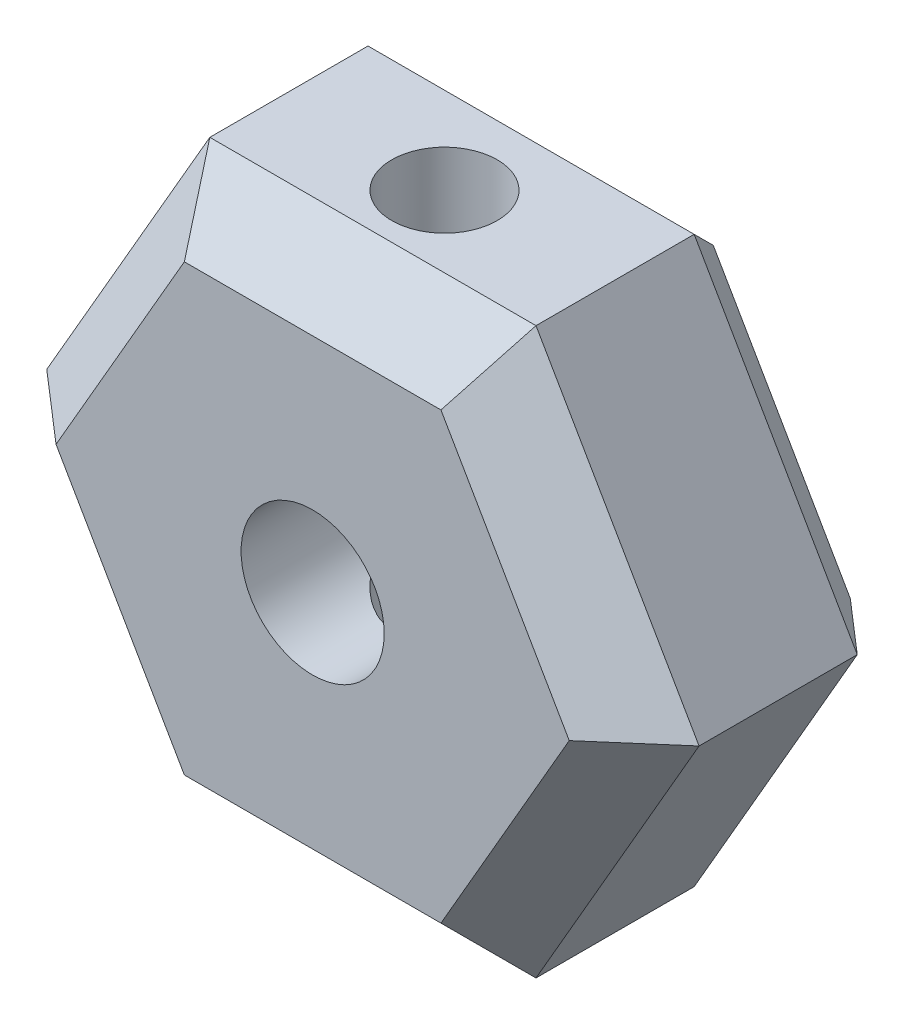
SolidWorks part; units mm, degrees
ref_plane "Front Plane" through (0, 0, 0) normal (0, 0, 1) x (1, 0, 0)
ref_plane "Top Plane" through (0, 0, 0) normal (0, 1, 0) x (1, 0, 0)
ref_plane "Right Plane" through (0, 0, 0) normal (1, 0, 0) x (0, 0, -1)
sketch "Sketch1" plane through (0, 0, 0) normal (0, 0, 1) x (1, 0, 0)
  line L1 (8.6603, 0) -> (4.3301, 7.5)
  line L2 (4.3301, 7.5) -> (-4.3301, 7.5)
  line L3 (-4.3301, 7.5) -> (-8.6603, 0)
  line L4 (-8.6603, 0) -> (-4.3301, -7.5)
  line L5 (-4.3301, -7.5) -> (4.3301, -7.5)
  line L6 (4.3301, -7.5) -> (8.6603, 0)
  circle A0 centre (0, 0) radius 7.5 construction
  circle A1 centre (0, 0) radius 1.9
  dimension "D1" = 3.8
  dimension "D2" = 15
extrude "Boss-Extrude1" add sketch "Sketch1" along normal blind 7
sketch "Sketch2" plane through (0, -7.5, 0) normal (0, -1, 0) x (1, 0, 0)
  line L0 (-4.3301, 3.5) -> (4.3301, 3.5) construction
  line L1 (-4.3301, 7) -> (-4.3301, 0) construction
  line L2 (4.3301, 7) -> (4.3301, 0) construction
  circle A0 centre (0, 3.5) radius 1.4
  dimension "D1" = 2.8
extrude "Cut-Extrude1" cut sketch "Sketch2" against normal through all
chamfer "Chamfer1" distance 1.6 angle 45 6 edges at (-6.4952, -3.75, 7) (0, -7.5, 7) (6.4952, -3.75, 7) (6.4952, 3.75, 7) (0, 7.5, 7) (-6.4952, 3.75, 7)
chamfer "Chamfer2" distance 1.2 angle 45 6 edges at (0, 7.5, 0) (6.4952, 3.75, 0) (6.4952, -3.75, 0) (0, -7.5, 0) (-6.4952, -3.75, 0) (-6.4952, 3.75, 0)
